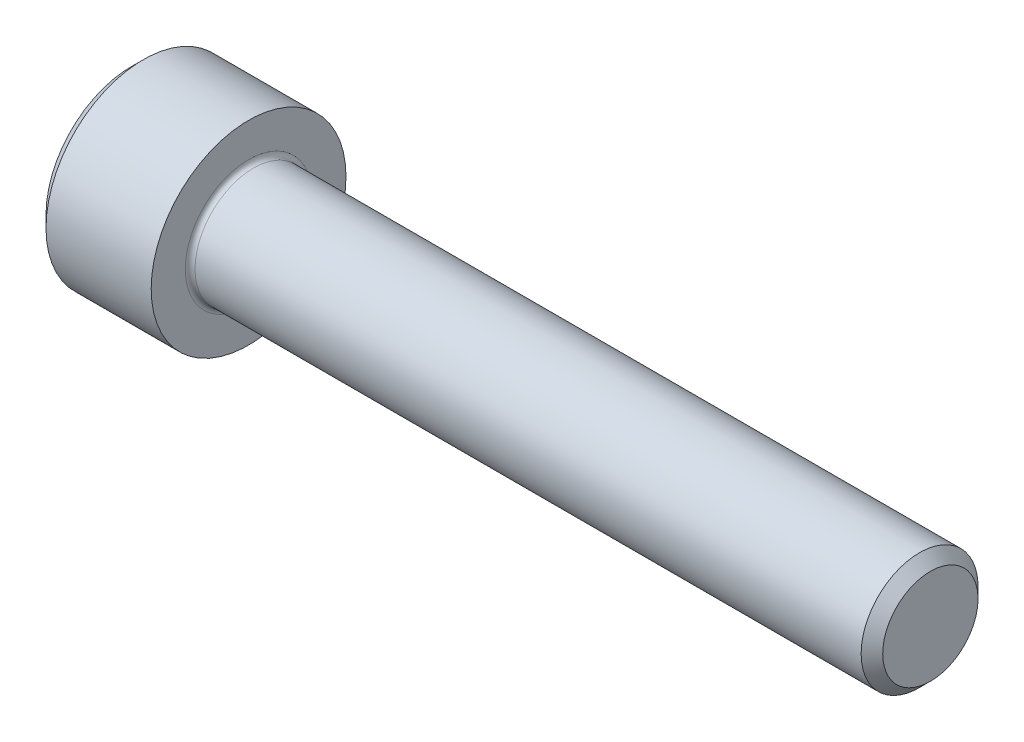
SolidWorks part; units mm, degrees
revolve "Base-Revolve" add sketch "BodySke"
sketch "BodySke" plane through (0, 0, 0) normal (0, 0, 1) x (1, 0, 0)
  line L0 (0, 0) -> (0, 4.4)
  line L1 (0.6, 5) -> (6, 5)
  line L2 (6, 5) -> (6, 3)
  line L3 (6, 3) -> (40.4455, 3)
  line L4 (41, 2.4455) -> (41, 0)
  line L5 (41, 0) -> (0, 0)
  line L6 (-31.75, 0) -> (127, 0) construction
  line L7 (0, 4.4) -> (0.6, 5)
  line L8 (41, 2.4455) -> (40.4455, 3)
  line L9 (0, -4.4) -> (0.6, -5) construction
  line L10 (41, -2.4455) -> (40.4455, -3) construction
  line L11 (7, 9.525) -> (7, 3.175) construction
  line L12 (17, 9.525) -> (17, 3.175) construction
  line L13 (-9, 9.525) -> (-9, 3.175) construction
  dimension "Diameter" = 6
  dimension "Head_ht" = 6
  dimension "Length" = 35
  dimension "Body_ch_ang" = 45
  dimension "Head_dia" = 10
  dimension "Head_ch_ang" = 45
  dimension "Minor_dia" = 4.891
  dimension "Advance" = 1
  dimension "Thread_nom" = 24
  dimension "Thread_length" = 50
  dimension "Head_ch_ht" = 0.6
cosmetic thread "ThreadCosmetic"
fillet "Fillet1" radius 0.25 1 edges at (6, 0, 3)
ref_plane "Plane1" through (0, 0, 0) normal (0, 0, 1) x (1, 0, 0)
ref_plane "Plane2" through (0, 0, 0) normal (0, 1, 0) x (1, 0, 0)
ref_plane "Plane3" through (0, 0, 0) normal (1, 0, 0) x (0, 0, -1)
sketch "Sketch2" plane through (0, 0, 0) normal (0, 0, 1) x (1, 0, 0)
  line L0 (0, 2.542) -> (3, 2.542)
  line L1 (3, 2.542) -> (4.4676, 0)
  line L2 (-31.75, 0) -> (127, 0) construction
  line L3 (4.4676, 0) -> (0, 0)
  line L4 (0, 0) -> (0, 2.542)
  line L5 (0, 4.4) -> (0, -4.4) construction
  line L6 (0, 0) -> (47.625, 0) construction
  line L7 (6, -5) -> (6, 5) construction
  dimension "D1" = 2.542
  dimension "D2" = 60
revolve "Hex-PreBroach" cut sketch "Sketch2" angle 360 about L6
sketch "Sketch3" plane through (0, 0, 0) normal (-1, 0, 0) x (0, 0.5, 0.866)
  line L0 (1.4676, 2.542) -> (-1.4676, 2.542)
  line L1 (-1.4676, 2.542) -> (-2.9352, 0)
  line L2 (1.4676, 2.542) -> (2.9352, 0)
  line L3 (1.4676, -2.542) -> (2.9352, 0)
  line L4 (1.4676, -2.542) -> (-1.4676, -2.542)
  line L5 (-1.4676, -2.542) -> (-2.9352, 0)
  dimension "D1" = 2.542
  dimension "D2" = 2.542
  dimension "Hex_size" = 5.084
extrude "Hex" cut sketch "Sketch3" against normal blind 3
sketch "Sketch4" plane through (0, 0, 0) normal (-1, 0, 0) x (0, 0, 1)
  line L0 (0, 0) -> (2.8067, 0)
  line L1 (0, 0) -> (6.1484, 3.5498) construction
  line L2 (0, 0) -> (1.4033, 2.4307)
  line L3 (2.3336, 0.614) -> (2.6851, 0.817)
  line L4 (1.6986, 1.7139) -> (2.0501, 1.9169)
  arc A0 (2.3336, 0.614) -> (1.6986, 1.7139) centre (0, 0) ccw
  arc A1 (2.8067, 0) -> (2.6851, 0.817) centre (0, 0) ccw
  arc A2 (1.4033, 2.4307) -> (2.0501, 1.9169) centre (0, 0) cw
  dimension "D1" = 30
  dimension "D2" = 60
  dimension "Spline_p_dim" = 1.27
  dimension "D3" = 0.635
extrude "Spline" [suppressed] cut sketch "Sketch4" against normal blind 3
pattern_circular "CirPattern1" [suppressed] count 6 every 60
sketch "Sketch5" plane through (0, 0, 0) normal (0, 0, 1) x (1, 0, 0)
  line L0 (-31.75, 0) -> (127, 0) construction
  line L2 (0, 4.4) -> (0, -4.4) construction
  circle A0 centre (2.3, 0) radius 0.675
  dimension "Drilled_hole_dia" = 1.35
  dimension "Drilled_hole_loc" = 2.3
extrude "Hole" [suppressed] cut sketch "Sketch5" against normal through all and the other way through all
pattern_circular "Drilled-4" [suppressed] count 2 every 60
pattern_circular "Drilled-6" [suppressed] count 3 every 60
sketch "ThdSchSke" plane through (0, 0, 0) normal (0, 0, 1) x (1, 0, 0)
  line L0 (17, -2.4455) -> (16.6117, -3)
  line L1 (17, -2.4455) -> (17.3883, -3)
  line L2 (17.3883, -3) -> (17.3883, -3.75)
  line L3 (-3.175, 0) -> (5.1513, 0) construction
  line L5 (17.3883, -3.75) -> (16.6117, -3.75)
  line L6 (16.6117, -3.75) -> (16.6117, -3)
  line L7 (0, 4.4) -> (0, -4.4) construction
  dimension "Thread_minor" = 4.891
  dimension "Diameter" = 6
  dimension "Start" = 17
revolve "ThreadSchematic" [suppressed] cut sketch "ThdSchSke" angle 360 about L3
pattern_linear "ThdSchPat" [suppressed]
equation "\"D2@Sketch3\" = \"Hex_size@Sketch3\" / 2"
equation "\"D1@Sketch3\" = \"Hex_size@Sketch3\" / 2"
equation "\"D1@Sketch2\" = \"Hex_size@Sketch3\" / 2"
equation "\"D3@Sketch4\" = \"Spline_p_dim@Sketch4\" / 2"
equation "\"Thread_minor@ThreadCosmetic\"  =  \"Minor_dia@BodySke\""
equation "\"D2@CirPattern1\" = 360 / \"Num_teeth@CirPattern1\""
equation "\"Wall_thickness@Sketch2\" = \"Head_ht@BodySke\" - \"Key_eng@Hex\""
equation "\"Thread_length@ThreadCosmetic\" = ((sgn( (\"Length@BodySke\" - \"Advance@BodySke\" ) - \"Thread_nom@BodySke\" )-1)*( (\"Length@BodySke\" - \"Advance@BodySke\" ) - \"Thread_nom@BodySke\" ))/-2+ \"Thread_nom@BodySke\""
equation "\"Thread_minor@ThdSchSke\" = \"Minor_dia@BodySke\""
equation "\"Diameter@ThdSchSke\" = \"Diameter@BodySke\""
equation "\"Overcut@ThdSchSke\" = \"Diameter@BodySke\" * 1.25"
equation "\"Start@ThdSchSke\" = \"Head_ht@BodySke\" + \"Length@BodySke\" - \"Thread_length@ThreadCosmetic\"  '---Non-countersunk---"
equation "\"Num_threads@ThdSchPat\" = int( \"Thread_length@ThreadCosmetic\" / \"Advance@BodySke\" + 0.999 )  + 1"
equation "\"Advance@ThdSchPat\" = \"Thread_length@ThreadCosmetic\" /  (\"Num_threads@ThdSchPat\" - 1) 'relax it"
equation "\"Num_threads@ThdSchPat\" = \"Num_threads@ThdSchPat\" - sgn( \"Num_threads@ThdSchPat\" - 1) '---chamfered tips only---"
